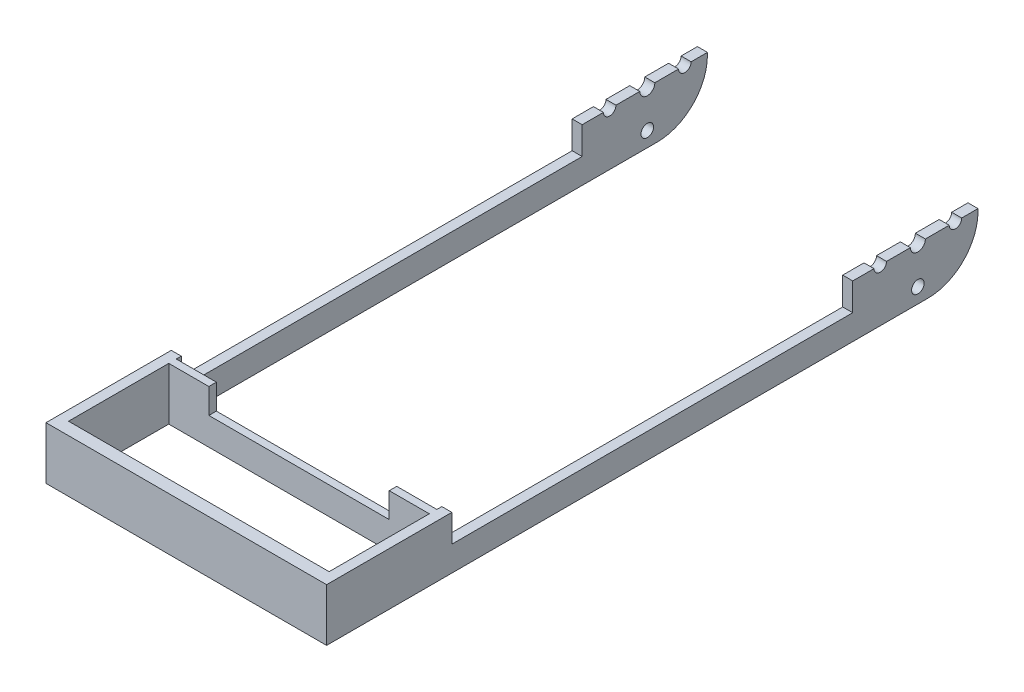
SolidWorks part; units mm, degrees
ref_plane "Front Plane" through (0, 0, 0) normal (0, 0, 1) x (1, 0, 0)
ref_plane "Top Plane" through (0, 0, 0) normal (0, 1, 0) x (1, 0, 0)
ref_plane "Right Plane" through (0, 0, 0) normal (1, 0, 0) x (0, 0, -1)
sketch "Sketch3" plane through (0, 0, 0) normal (0, 0, 1) x (1, 0, 0)
  line L1 (-28, 10.5) -> (28, 10.5)
  line L2 (-28, 10.5) -> (-28, -10.5)
  line L3 (-28, -10.5) -> (28, -10.5)
  line L4 (28, 10.5) -> (28, -10.5)
  line L5 (-28, 10.5) -> (28, -10.5) construction
  line L6 (-28, -10.5) -> (28, 10.5) construction
  point P0 (0, 0)
  dimension "D1" = 56
  dimension "D2" = 21
extrude "Boss-Extrude1" add sketch "Sketch3" along normal blind 130
sketch "Sketch4" plane through (0, -10.5, 0) normal (0, -1, 0) x (1, 0, 0)
  line L0 (0, 0) -> (0, 35) construction
  line L1 (26, 0) -> (26, 106)
  line L2 (26, 107.5) -> (26, 127.5)
  line L7 (-28, 0) -> (28, 0) construction
  line L8 (26, 127.5) -> (-26, 127.5)
  line L9 (-26, 127.5) -> (-26, 107.5)
  line L10 (-26, 106) -> (-26, 0)
  line L11 (-26, 0) -> (26, 0)
  line L12 (28, 130) -> (28, 0) construction
  line L13 (-28, 130) -> (-28, 0) construction
  line L14 (-28, 130) -> (28, 130) construction
  line L15 (-26, 107.5) -> (26, 107.5)
  line L16 (-26, 106) -> (26, 106)
  dimension "D1" = 35
  dimension "D2" = 2
  dimension "D3" = 2
  dimension "D4" = 2.5
  dimension "D5" = 1.5
  dimension "D6" = 20
extrude "Cut-Extrude3" cut sketch "Sketch4" against normal through all
sketch "Sketch6" plane through (28, 0, 0) normal (1, 0, 0) x (0, 0, -1)
  line L0 (0, -10.5) -> (0, 10.5) construction
  line L1 (0, 0) -> (-22.8922, 0) construction
  line L2 (-12, 0) -> (-12, 9.1156) construction
  line L3 (-12, 0) -> (-12, 6.3751) construction
  circle A0 centre (-12, 0) radius 1.5
  circle A7 centre (-4.5, 0) radius 1.25
  circle A8 centre (-19.5, 0) radius 1.25
  circle A9 centre (-12, 7.5) radius 1.25
  circle A10 centre (-12, -7.5) radius 1.25
  point P19 (-9, 0)
  dimension "D1" = 12
  dimension "D2" = 3
  dimension "D3" = 2.5
  dimension "D4" = 7.5
  dimension "D5" = 2.5
  dimension "D6" = 7.5
extrude "Cut-Extrude4" cut sketch "Sketch6" against normal through all
fillet "Fillet1" radius 10 4 edges at (27, 10.5, 0) (27, -10.5, 0) (-27, 10.5, 0) (-27, -10.5, 0)
sketch "Sketch7" plane through (28, 0, 0) normal (1, 0, 0) x (0, 0, -1)
  line L0 (-130, -10.5) -> (-130, 10.5) construction
  line L1 (-105, 4.5) -> (-25, 4.5)
  line L2 (-105, 4.5) -> (-105, -5.5)
  line L3 (-105, -5.5) -> (-25, -5.5)
  line L4 (-25, 4.5) -> (-25, -5.5)
  line L5 (-105, 4.5) -> (-25, -5.5) construction
  line L6 (-105, -5.5) -> (-25, 4.5) construction
  line L7 (-130, -10.5) -> (-10, -10.5) construction
  point P0 (-65, -0.5)
  dimension "D1" = 80
  dimension "D2" = 10
  dimension "D3" = 65
  dimension "D4" = 10
extrude "Cut-Extrude5" cut sketch "Sketch7" against normal through all
sketch "Sketch8" plane through (0, 0, 106) normal (0, 0, -1) x (-1, 0, 0)
  line L1 (-18, 5) -> (18, 5)
  line L2 (-18, 5) -> (-18, -5)
  line L3 (-18, -5) -> (18, -5)
  line L4 (18, 5) -> (18, -5)
  line L5 (-18, 5) -> (18, -5) construction
  line L6 (-18, -5) -> (18, 5) construction
  point P0 (0, 0)
  dimension "D1" = 36
  dimension "D2" = 10
extrude "Cut-Extrude6" cut sketch "Sketch8" against normal blind 2
sketch "Sketch9" plane through (28, 0, 0) normal (1, 0, 0) x (0, 0, -1)
  line L0 (-12, 0) -> (-148.1228, 0) construction
  line L1 (8.3285, 0) -> (-140.6482, 0)
  line L2 (-140.6482, 0) -> (-140.6482, 18.171)
  line L3 (-140.6482, 18.171) -> (9.875, 18.171)
  line L4 (9.875, 18.171) -> (9.875, 0)
  line L5 (9.875, 0) -> (8.3285, 0)
extrude "Cut-Extrude7" cut sketch "Sketch9" against normal through all
